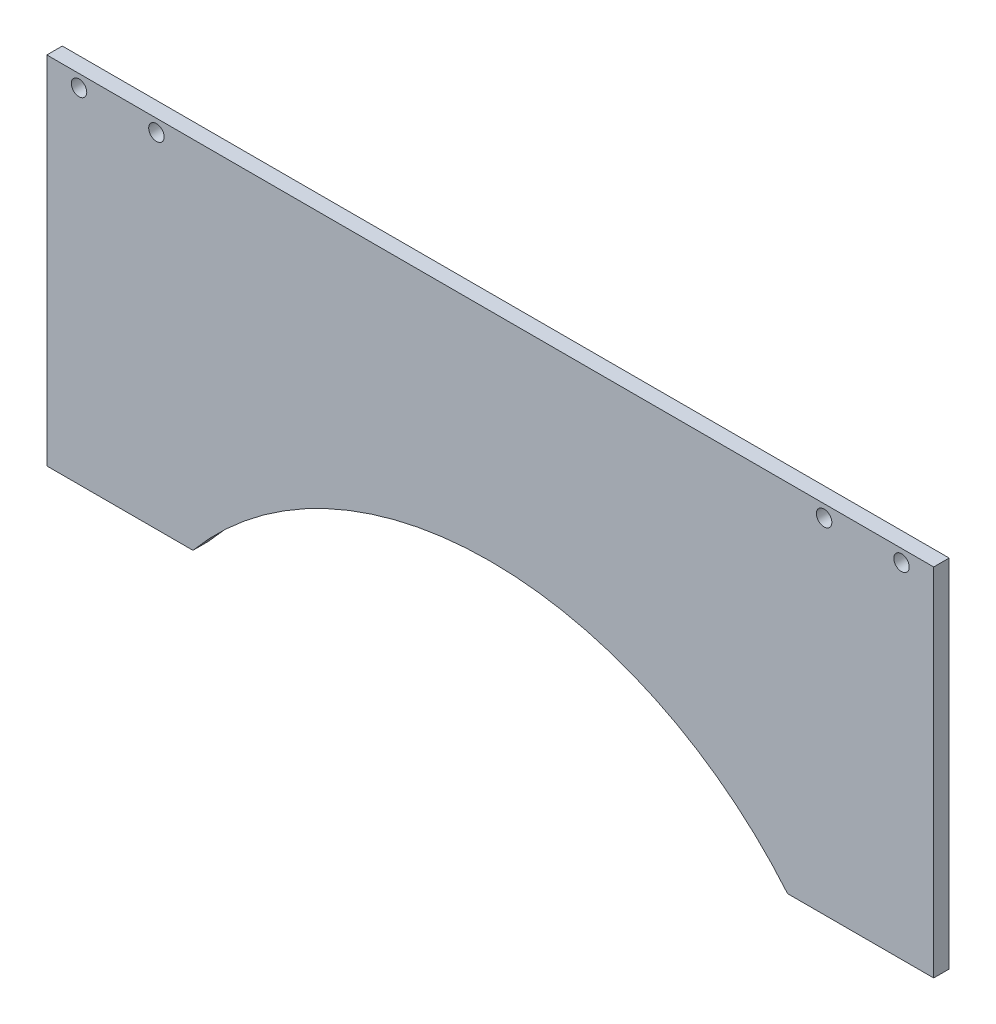
SolidWorks part; units mm, degrees
material "Acrylic (Medium-high impact)"
ref_plane "Front Plane" through (0, 0, 0) normal (0, 0, 1) x (1, 0, 0)
ref_plane "Top Plane" through (0, 0, 0) normal (0, 1, 0) x (1, 0, 0)
ref_plane "Right Plane" through (0, 0, 0) normal (1, 0, 0) x (0, 0, -1)
sketch "Sketch6" plane through (0, 0, 0) normal (0, 0, 1) x (1, 0, 0)
  line L0 (-125, 0) -> (161.5, 0)
  line L1 (-125, 115) -> (161.5, 115)
  line L2 (-125, 115) -> (-125, 0)
  line L4 (161.5, 115) -> (161.5, 0)
  line L5 (-125, 115) -> (0, 0) construction
  line L6 (0, 0) -> (161.5, 115) construction
  point P0 (0, 0)
  dimension "D1" = 286.5
  dimension "D2" = 115
extrude "Boss-Extrude3" add sketch "Sketch6" along normal blind 5
sketch "Sketch7" plane through (0, 0, 5) normal (0, 0, 1) x (1, 0, 0)
  line L0 (161.5, 0) -> (161.5, 115) construction
  line L1 (-125, 115) -> (-125, 0) construction
  line L2 (161.5, 115) -> (-125, 115) construction
  circle A0 centre (151.1, 111) radius 2.5
  circle A1 centre (126.1, 111) radius 2.5
  circle A2 centre (-114.6, 111) radius 2.5
  circle A3 centre (-89.6, 111) radius 2.5
  dimension "D1" = 5
  dimension "D3" = 25
  dimension "D4" = 10.4
  dimension "D2" = 10.4
  dimension "D5" = 25
  dimension "D6" = 4
  dimension "D7" = 4
  dimension "D8" = 4
extrude "Cut-Extrude1" cut sketch "Sketch7" against normal blind 13
sketch "Sketch8" plane through (0, 0, 5) normal (0, 0, 1) x (1, 0, 0)
  line L0 (161.5, 0) -> (161.5, 115) construction
  line L3 (-125, 0) -> (161.5, 0) construction
  circle A2 centre (18.25, -80) radius 125
  dimension "D1" = 250
  dimension "D2" = 143.25
  dimension "D3" = 80
extrude "Cut-Extrude4" cut sketch "Sketch8" against normal blind 10
